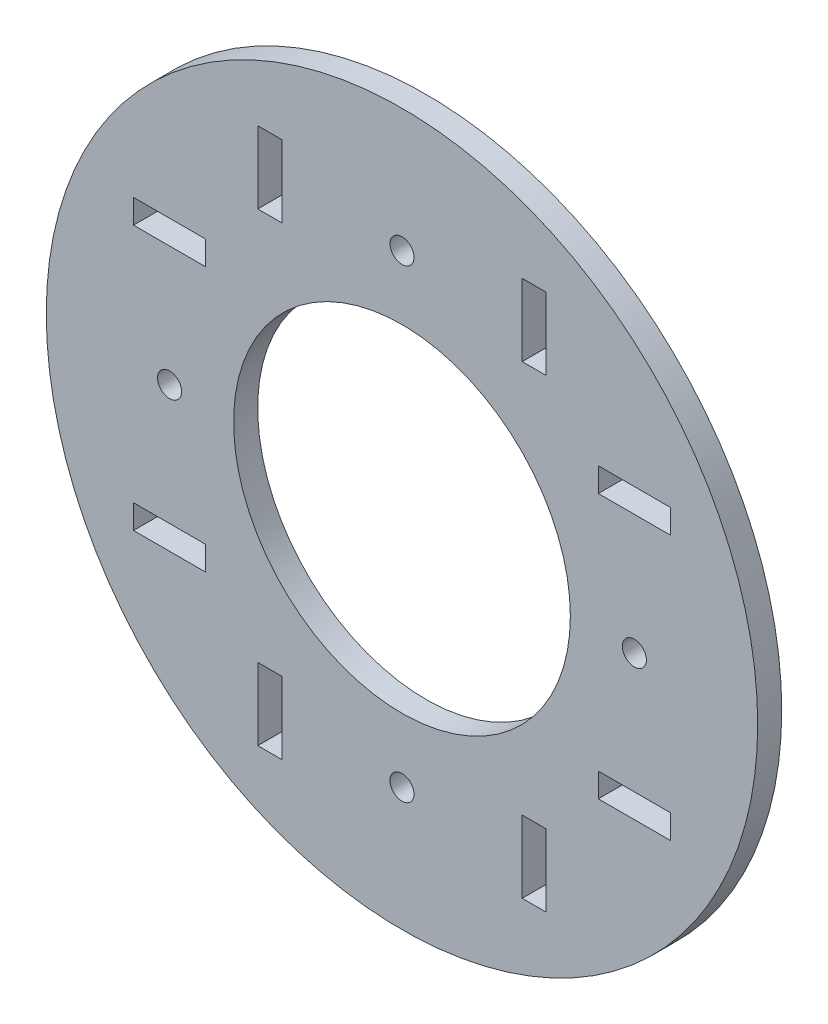
SolidWorks part; units mm, degrees
material "ABS"
ref_plane "Front Plane" through (0, 0, 0) normal (0, 0, 1) x (1, 0, 0)
ref_plane "Top Plane" through (0, 0, 0) normal (0, 1, 0) x (1, 0, 0)
ref_plane "Right Plane" through (0, 0, 0) normal (1, 0, 0) x (0, 0, -1)
sketch "Sketch2" plane through (0, 0, 0) normal (0, 0, 1) x (1, 0, 0)
  line L0 (-19.05, -35.4597) -> (-15.875, -35.4597)
  line L1 (-19.05, 32.2847) -> (-19.05, 35.4597)
  line L3 (-19.05, 32.2847) -> (-19.05, 25.9347)
  line L4 (-15.875, -35.4597) -> (-15.875, -25.9347)
  line L5 (-15.875, 25.9347) -> (-19.05, 25.9347)
  line L6 (-15.875, 35.4597) -> (-15.875, 25.9347)
  line L7 (-19.05, 35.4597) -> (-15.875, 35.4597)
  line L8 (-15.875, -25.9347) -> (-19.05, -25.9347)
  line L9 (19.05, 35.4597) -> (15.875, 35.4597)
  line L10 (15.875, 35.4597) -> (15.875, 25.9347)
  line L11 (15.875, 25.9347) -> (19.05, 25.9347)
  line L12 (19.05, 32.2847) -> (19.05, 35.4597)
  line L13 (19.05, -32.2847) -> (19.05, -25.9347)
  line L14 (19.05, 32.2847) -> (19.05, 25.9347)
  line L15 (19.05, -32.2847) -> (19.05, -35.4597)
  line L16 (-35.4597, -19.05) -> (-35.4597, -15.875)
  line L17 (-35.4597, -15.875) -> (-25.9347, -15.875)
  line L18 (15.875, -25.9347) -> (19.05, -25.9347)
  line L19 (15.875, -35.4597) -> (15.875, -25.9347)
  line L20 (19.05, -35.4597) -> (15.875, -35.4597)
  line L22 (-25.9347, -15.875) -> (-25.9347, -19.05)
  line L23 (-32.2847, 19.05) -> (-35.4597, 19.05)
  line L24 (-32.2847, 19.05) -> (-25.9347, 19.05)
  line L25 (-25.9347, 15.875) -> (-25.9347, 19.05)
  line L26 (-35.4597, 15.875) -> (-25.9347, 15.875)
  line L27 (-35.4597, 19.05) -> (-35.4597, 15.875)
  line L28 (-19.05, -32.2847) -> (-19.05, -35.4597)
  line L29 (35.4597, 19.05) -> (35.4597, 15.875)
  line L30 (25.9347, 15.875) -> (25.9347, 19.05)
  line L31 (32.2847, 19.05) -> (25.9347, 19.05)
  line L32 (-19.05, -32.2847) -> (-19.05, -25.9347)
  line L33 (32.2847, 19.05) -> (35.4597, 19.05)
  line L34 (35.4597, 15.875) -> (25.9347, 15.875)
  line L35 (32.2847, -19.05) -> (35.4597, -19.05)
  line L36 (32.2847, -19.05) -> (25.9347, -19.05)
  line L37 (25.9347, -15.875) -> (25.9347, -19.05)
  line L38 (35.4597, -15.875) -> (25.9347, -15.875)
  line L39 (35.4597, -19.05) -> (35.4597, -15.875)
  line L51 (-32.2847, -19.05) -> (-25.9347, -19.05)
  line L54 (-32.2847, -19.05) -> (-35.4597, -19.05)
  circle A0 centre (0, 0) radius 46.99
  circle A1 centre (0, -30.6972) radius 1.5875
  circle A2 centre (0, 30.6972) radius 1.5875
  circle A3 centre (30.6972, 0) radius 1.5875
  circle A4 centre (-30.6972, 0) radius 1.5875
  circle A5 centre (0, 0) radius 22.2408
  dimension "D1" = 93.98
  dimension "D2" = 3.175
  dimension "D3" = 3.175
  dimension "D4" = 3.175
  dimension "D5" = 3.175
extrude "Boss-Extrude1" add sketch "Sketch2" along normal blind 3.175
